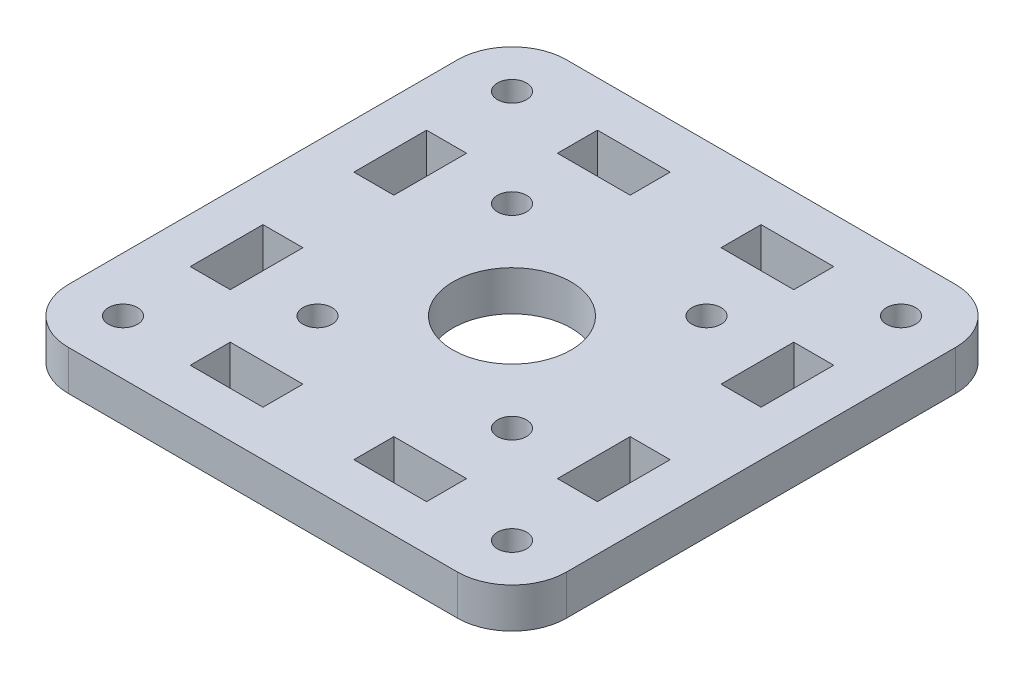
SolidWorks part; units mm, degrees
ref_plane "前视基准面" through (0, 0, 0) normal (0, 0, 1) x (1, 0, 0)
ref_plane "上视基准面" through (0, 0, 0) normal (0, 1, 0) x (1, 0, 0)
ref_plane "右视基准面" through (0, 0, 0) normal (1, 0, 0) x (0, 0, -1)
sketch "草图1" plane through (0, 0, 0) normal (0, 1, 0) x (1, 0, 0)
  line L0 (0, 0) -> (27.4, 27.4) construction
  line L1 (-27.4, 27.4) -> (27.4, 27.4)
  line L2 (-27.4, 27.4) -> (-27.4, -27.4)
  line L3 (-27.4, -27.4) -> (27.4, -27.4)
  line L4 (27.4, 27.4) -> (27.4, -27.4)
  line L5 (0, -27.4) -> (0, 27.4) construction
  line L6 (-27.4, 0) -> (27.4, 0) construction
  line L7 (18, -5) -> (18, 5) construction
  line L8 (18, 5) -> (22.4, 5)
  line L9 (22.4, 5) -> (22.4, -5) construction
  line L10 (18, 5) -> (18, 13)
  line L11 (18, 13) -> (22.4, 13)
  line L12 (22.4, 13) -> (22.4, 5)
  line L13 (0, 0) -> (27.4, -27.4) construction
  line L14 (22.4, -13) -> (22.4, -5)
  line L15 (18, -13) -> (22.4, -13)
  line L16 (18, -5) -> (18, -13)
  line L17 (18, -5) -> (22.4, -5)
  line L18 (-22.4, 5) -> (-22.4, -5) construction
  line L19 (-18, -5) -> (-18, 5) construction
  line L20 (-18, -5) -> (-22.4, -5)
  line L21 (-18, -5) -> (-18, -13)
  line L22 (-18, -13) -> (-22.4, -13)
  line L23 (-22.4, -13) -> (-22.4, -5)
  line L24 (-22.4, 13) -> (-22.4, 5)
  line L25 (-18, 13) -> (-22.4, 13)
  line L26 (-18, 5) -> (-18, 13)
  line L27 (-18, 5) -> (-22.4, 5)
  line L28 (0, 0) -> (-27.4, -27.4) construction
  line L29 (0, 0) -> (-27.4, 27.4) construction
  line L30 (13, 22.4) -> (5, 22.4)
  line L31 (13, 18) -> (13, 22.4)
  line L32 (5, 18) -> (13, 18)
  line L33 (5, 18) -> (5, 22.4)
  line L34 (5, -18) -> (5, -22.4)
  line L35 (5, -18) -> (13, -18)
  line L36 (13, -18) -> (13, -22.4)
  line L37 (13, -22.4) -> (5, -22.4)
  line L38 (-13, -22.4) -> (-5, -22.4)
  line L39 (-13, -18) -> (-13, -22.4)
  line L40 (-5, -18) -> (-13, -18)
  line L41 (-5, -18) -> (-5, -22.4)
  line L42 (-5, 18) -> (-5, 22.4)
  line L43 (-5, 18) -> (-13, 18)
  line L44 (-13, 18) -> (-13, 22.4)
  line L45 (-13, 22.4) -> (-5, 22.4)
  line L46 (18, 13) -> (18, 18) construction
  circle A0 centre (0, 0) radius 6.5
  circle A1 centre (21.4, 21.4) radius 1.6
  circle A2 centre (21.4, -21.4) radius 1.6
  circle A3 centre (-21.4, -21.4) radius 1.6
  circle A4 centre (-21.4, 21.4) radius 1.6
  point P17 (22.4, 0)
  point P18 (18, 0)
  point P32 (-18, 0)
  point P33 (-22.4, 0)
  dimension "D1" = 13
  dimension "D8" = 3.2
  dimension "D2" = 45
  dimension "D3" = 4.4
  dimension "D4" = 18
  dimension "D5" = 10
  dimension "D6" = 8
  dimension "D7" = 5
  dimension "D9" = 6
extrude "凸台-拉伸1" add sketch "草图1" along normal blind 4.4
fillet "圆角1" radius 6 4 edges at (-27.4, 2.2, 27.4) (-27.4, 2.2, -27.4) (27.4, 2.2, -27.4) (27.4, 2.2, 27.4)
sketch "草图2" plane through (0, 4.4, 0) normal (0, 1, 0) x (1, 0, 0)
  line L0 (0, 0) -> (21.4, 21.4) construction
  line L1 (0, 0) -> (21.4, -21.4) construction
  line L2 (0, 0) -> (-21.4, -21.4) construction
  line L3 (0, 0) -> (-21.4, 21.4) construction
  circle A0 centre (10.7, 10.7) radius 1.6
  circle A1 centre (10.7, -10.7) radius 1.6
  circle A2 centre (-10.7, -10.7) radius 1.6
  circle A3 centre (-10.7, 10.7) radius 1.6
  point P17 (0, 0)
  dimension "D1" = 3.2
  dimension "D2" = 4
extrude "切除-拉伸1" cut sketch "草图2" against normal blind 10
sketch "草图3" plane through (0, 0, 0) normal (0, 0, 1) x (1, 0, 0)
